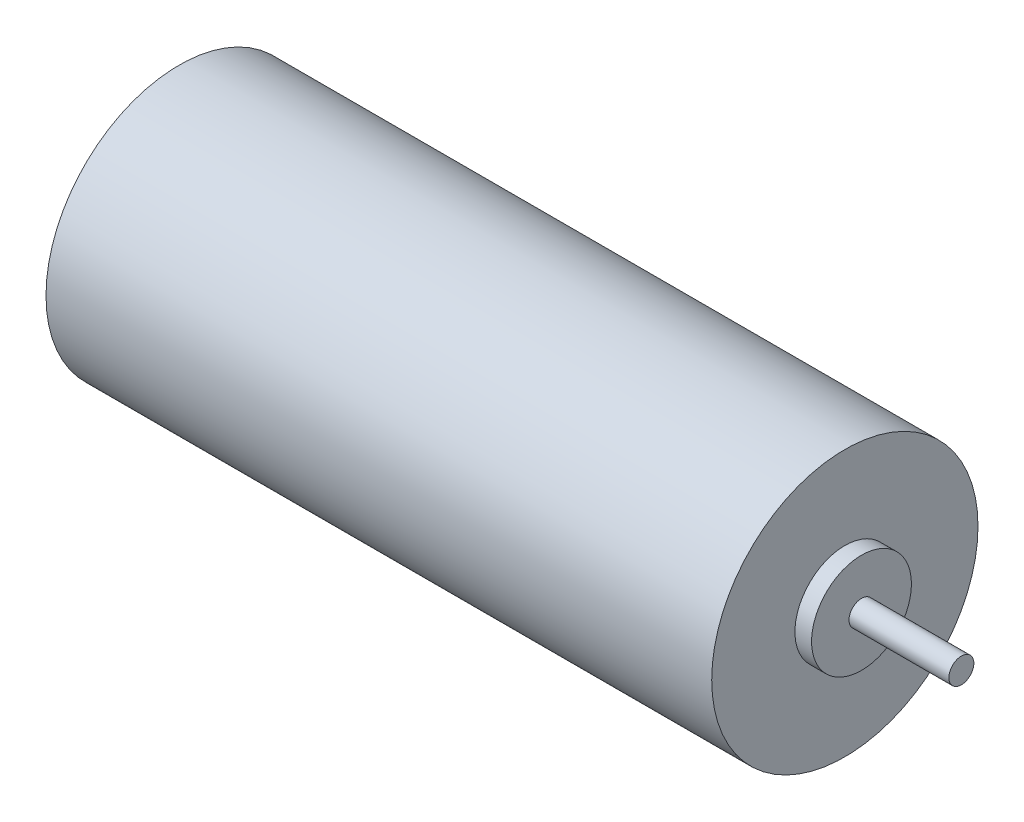
SolidWorks part; units mm, degrees
ref_plane "Front Plane" through (0, 0, 0) normal (0, 0, 1) x (1, 0, 0)
ref_plane "Top Plane" through (0, 0, 0) normal (0, 1, 0) x (1, 0, 0)
ref_plane "Right Plane" through (0, 0, 0) normal (1, 0, 0) x (0, 0, -1)
sketch "Sketch1" plane through (0, 0, 0) normal (1, 0, 0) x (0, 0, -1)
  circle A0 centre (0, 0) radius 8
extrude "Boss-Extrude1" add sketch "Sketch1" along normal blind 40
sketch "Sketch2" plane through (40, 0, 0) normal (1, 0, 0) x (0, 0, -1)
  circle A0 centre (0, 0) radius 3
extrude "Boss-Extrude2" add sketch "Sketch2" along normal blind 1
sketch "Sketch3" plane through (41, 0, 0) normal (1, 0, 0) x (0, 0, -1)
  circle A0 centre (0, 0) radius 0.75
extrude "Boss-Extrude3" add sketch "Sketch3" along normal blind 6
